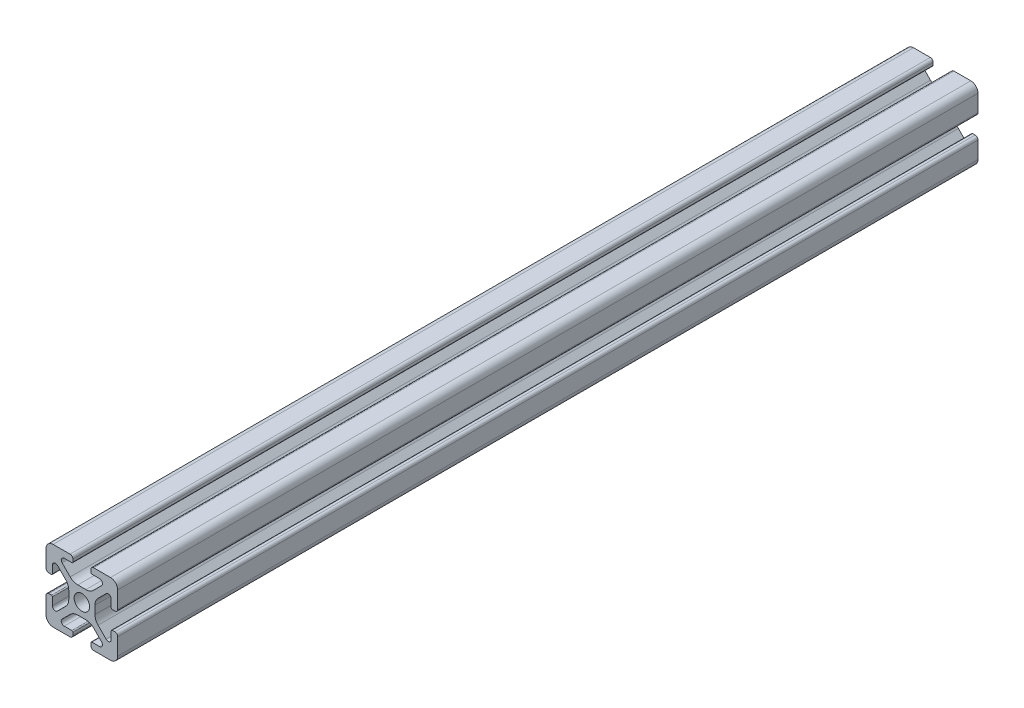
SolidWorks part; units mm, degrees
ref_plane "Front Plane" through (0, 0, 0) normal (0, 0, 1) x (1, 0, 0)
ref_plane "Top Plane" through (0, 0, 0) normal (0, 1, 0) x (1, 0, 0)
ref_plane "Right Plane" through (0, 0, 0) normal (1, 0, 0) x (0, 0, -1)
ref_plane "Plane1" through (0, 0, 0) normal (0, 0, -1) x (-1, 0, 0)
sketch "Sketch1" plane through (0, 0, 0) normal (0, 0, -1) x (-1, 0, 0)
  line L0 (-12.5, 0.8) -> (-12.5, 1.5)
  line L1 (-12.8, 1.8) -> (-14.9176, 1.8)
  line L2 (-15.5062, 3.221) -> (-13.2559, 5.4713)
  line L3 (-11.1346, 6.35) -> (-8.8654, 6.35)
  line L4 (-6.7441, 5.4713) -> (-4.4938, 3.221)
  line L5 (-5.0824, 1.8) -> (-7.2, 1.8)
  line L6 (-7.5, 1.5) -> (-7.5, 0.8)
  line L7 (-6.7, 0) -> (-2, 0)
  line L8 (0, 2) -> (0, 6.7)
  line L9 (-0.8, 7.5) -> (-1.5, 7.5)
  line L10 (-1.8, 7.2) -> (-1.8, 5.0824)
  line L11 (-3.221, 4.4938) -> (-5.4713, 6.7441)
  line L12 (-6.35, 8.8654) -> (-6.35, 11.1346)
  line L13 (-5.4713, 13.2559) -> (-3.221, 15.5062)
  line L14 (-1.8, 14.9176) -> (-1.8, 12.8)
  line L15 (-1.5, 12.5) -> (-0.8, 12.5)
  line L16 (0, 13.3) -> (0, 18)
  line L17 (-2, 20) -> (-6.7, 20)
  line L18 (-7.5, 19.2) -> (-7.5, 18.5)
  line L19 (-7.2, 18.2) -> (-5.0824, 18.2)
  line L20 (-4.4938, 16.779) -> (-6.7441, 14.5287)
  line L21 (-8.8654, 13.65) -> (-11.1346, 13.65)
  line L22 (-13.2559, 14.5287) -> (-15.5062, 16.779)
  line L23 (-14.9176, 18.2) -> (-12.8, 18.2)
  line L24 (-12.5, 18.5) -> (-12.5, 19.2)
  line L25 (-13.3, 20) -> (-18, 20)
  line L26 (-20, 18) -> (-20, 13.3)
  line L27 (-19.2, 12.5) -> (-18.5, 12.5)
  line L28 (-18.2, 12.8) -> (-18.2, 14.9176)
  line L29 (-16.779, 15.5062) -> (-14.5287, 13.2559)
  line L30 (-13.65, 11.1346) -> (-13.65, 8.8654)
  line L31 (-14.5287, 6.7441) -> (-16.779, 4.4938)
  line L32 (-18.2, 5.0824) -> (-18.2, 7.2)
  line L33 (-18.5, 7.5) -> (-19.2, 7.5)
  line L34 (-20, 6.7) -> (-20, 2)
  line L35 (-18, 0) -> (-13.3, 0)
  arc A0 (-12.5, 1.5) -> (-12.8, 1.8) centre (-12.8, 1.5) ccw
  arc A1 (-14.9176, 1.8) -> (-15.5062, 3.221) centre (-14.9176, 2.6324) cw
  arc A2 (-13.2559, 5.4713) -> (-11.1346, 6.35) centre (-11.1346, 3.35) cw
  arc A3 (-8.8654, 6.35) -> (-6.7441, 5.4713) centre (-8.8654, 3.35) cw
  arc A4 (-4.4938, 3.221) -> (-5.0824, 1.8) centre (-5.0824, 2.6324) cw
  arc A5 (-7.2, 1.8) -> (-7.5, 1.5) centre (-7.2, 1.5) ccw
  arc A6 (-7.5, 0.8) -> (-6.7, 0) centre (-6.7, 0.8) ccw
  arc A7 (-2, 0) -> (0, 2) centre (-2, 2) ccw
  arc A8 (0, 6.7) -> (-0.8, 7.5) centre (-0.8, 6.7) ccw
  arc A9 (-1.5, 7.5) -> (-1.8, 7.2) centre (-1.5, 7.2) ccw
  arc A10 (-1.8, 5.0824) -> (-3.221, 4.4938) centre (-2.6324, 5.0824) cw
  arc A11 (-5.4713, 6.7441) -> (-6.35, 8.8654) centre (-3.35, 8.8654) cw
  arc A12 (-6.35, 11.1346) -> (-5.4713, 13.2559) centre (-3.35, 11.1346) cw
  arc A13 (-3.221, 15.5062) -> (-1.8, 14.9176) centre (-2.6324, 14.9176) cw
  arc A14 (-1.8, 12.8) -> (-1.5, 12.5) centre (-1.5, 12.8) ccw
  arc A15 (-0.8, 12.5) -> (0, 13.3) centre (-0.8, 13.3) ccw
  arc A16 (0, 18) -> (-2, 20) centre (-2, 18) ccw
  arc A17 (-6.7, 20) -> (-7.5, 19.2) centre (-6.7, 19.2) ccw
  arc A18 (-7.5, 18.5) -> (-7.2, 18.2) centre (-7.2, 18.5) ccw
  arc A19 (-5.0824, 18.2) -> (-4.4938, 16.779) centre (-5.0824, 17.3676) cw
  arc A20 (-6.7441, 14.5287) -> (-8.8654, 13.65) centre (-8.8654, 16.65) cw
  arc A21 (-11.1346, 13.65) -> (-13.2559, 14.5287) centre (-11.1346, 16.65) cw
  arc A22 (-15.5062, 16.779) -> (-14.9176, 18.2) centre (-14.9176, 17.3676) cw
  arc A23 (-12.8, 18.2) -> (-12.5, 18.5) centre (-12.8, 18.5) ccw
  arc A24 (-12.5, 19.2) -> (-13.3, 20) centre (-13.3, 19.2) ccw
  arc A25 (-18, 20) -> (-20, 18) centre (-18, 18) ccw
  arc A26 (-20, 13.3) -> (-19.2, 12.5) centre (-19.2, 13.3) ccw
  arc A27 (-18.5, 12.5) -> (-18.2, 12.8) centre (-18.5, 12.8) ccw
  arc A28 (-18.2, 14.9176) -> (-16.779, 15.5062) centre (-17.3676, 14.9176) cw
  arc A29 (-14.5287, 13.2559) -> (-13.65, 11.1346) centre (-16.65, 11.1346) cw
  arc A30 (-13.65, 8.8654) -> (-14.5287, 6.7441) centre (-16.65, 8.8654) cw
  arc A31 (-16.779, 4.4938) -> (-18.2, 5.0824) centre (-17.3676, 5.0824) cw
  arc A32 (-18.2, 7.2) -> (-18.5, 7.5) centre (-18.5, 7.2) ccw
  arc A33 (-19.2, 7.5) -> (-20, 6.7) centre (-19.2, 6.7) ccw
  arc A34 (-20, 2) -> (-18, 0) centre (-18, 2) ccw
  arc A35 (-13.3, 0) -> (-12.5, 0.8) centre (-13.3, 0.8) ccw
  circle A36 centre (-10, 10) radius 2.15
extrude "Boss-Extrude1" add sketch "Sketch1" against normal blind 240
equation "\"plate_thickness\" = 6.35 'thickness of the plate "
equation "\"t_height\" = 200"
equation "\"t_width\" = 240"
equation "\"t_length\" = 240"
equation "\"D1@Boss-Extrude1\"=\"t_width\""
equation "\"connector_D1\" = 70 'the big holes diameter"
equation "\"mtg_hole_D\" = 5.5 'mounting holes"
equation "\"mtg_dfc\" = 40 'mounting hole distance from center"
equation "\"plate_hole_from_edge\" = 9"
equation "\"plate_spacing\" = 1"
equation "\"front_plate_height\" = \"t_height\" + 38"
equation "\"front_plate_width\" = \"t_width\" + 38"
equation "\"side_plate_height\" = \"front_plate_height\""
equation "\"side_plate_length\" = \"t_length\" + 38"
equation "\"top_plate_width\" = \"front_plate_width\""
equation "\"top_plate_length\" = \"side_plate_length\""
equation "\"itx_support_t_slot_length\" = \"t_width\" + (2 * 20.5)"
equation "\"locomotion_length\" = \"t_length\""
equation "\"locomotion_width\" = \"t_width\""
equation "\"locomotion_height\" = 40"
